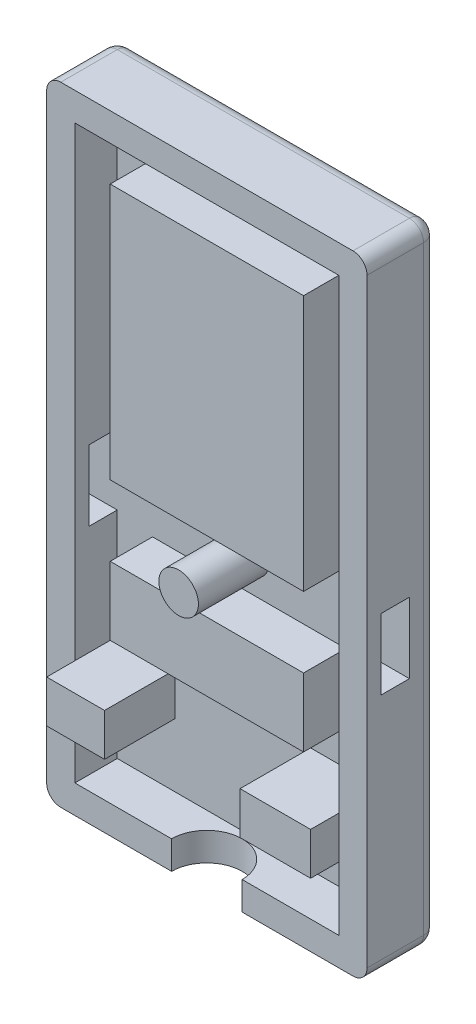
SolidWorks part; units mm, degrees
ref_plane "Front Plane" through (0, 0, 0) normal (0, 0, 1) x (1, 0, 0)
ref_plane "Top Plane" through (0, 0, 0) normal (0, 1, 0) x (1, 0, 0)
ref_plane "Right Plane" through (0, 0, 0) normal (1, 0, 0) x (0, 0, -1)
sketch "Sketch1" plane through (0, 0, 0) normal (0, 0, 1) x (1, 0, 0)
  line L1 (-11.35, 22.25) -> (11.35, 22.25)
  line L2 (-11.35, 22.25) -> (-11.35, -22.25)
  line L3 (-11.35, -22.25) -> (11.35, -22.25)
  line L4 (11.35, 22.25) -> (11.35, -22.25)
  line L5 (-11.35, 22.25) -> (11.35, -22.25) construction
  line L6 (-11.35, -22.25) -> (11.35, 22.25) construction
  point P0 (0, 0)
  dimension "D1" = 22.7
  dimension "D2" = 44.5
extrude "Boss-Extrude1" add sketch "Sketch1" along normal blind 2
sketch "Sketch2" plane through (0, 0, 2) normal (0, 0, 1) x (1, 0, 0)
  line L1 (-11.35, 22.25) -> (11.35, 22.25)
  line L2 (-11.35, 22.25) -> (-11.35, -22.25)
  line L3 (-11.35, -22.25) -> (11.35, -22.25)
  line L4 (11.35, 22.25) -> (11.35, -22.25)
  line L5 (-9.35, 20.25) -> (9.35, 20.25)
  line L6 (-9.35, 20.25) -> (-9.35, -20.25)
  line L7 (-9.35, -20.25) -> (9.35, -20.25)
  line L8 (9.35, 20.25) -> (9.35, -20.25)
  dimension "D1" = 2
  dimension "D2" = 2
  dimension "D3" = 2
  dimension "D4" = 2
extrude "Boss-Extrude2" add sketch "Sketch2" along normal blind 3
sketch "Sketch3" plane through (0, 0, 2) normal (0, 0, 1) x (1, 0, 0)
  line L0 (9.35, 20.25) -> (-9.35, 20.25) construction
  line L1 (-6.85, 19.25) -> (6.85, 19.25)
  line L2 (-6.85, 19.25) -> (-6.85, -12.75)
  line L3 (-6.85, -12.75) -> (6.85, -12.75)
  line L4 (6.85, 19.25) -> (6.85, -12.75)
  line L5 (9.35, -20.25) -> (9.35, 20.25) construction
  line L12 (-6.85, -12.75) -> (6.85, -12.75)
  line L15 (9.35, -13.15) -> (9.35, -15.75)
  line L16 (-9.35, 20.25) -> (-9.35, -20.25) construction
  line L17 (-9.35, -15.75) -> (-9.35, -13.15)
  line L19 (-6.85, -12.75) -> (-6.85, -7.5079)
  line L21 (-9.35, -12.75) -> (9.35, -12.75)
  line L22 (9.35, -12.75) -> (9.35, -13.15)
  line L23 (-9.35, -13.15) -> (-9.35, -12.75)
  line L24 (-9.35, -12.75) -> (-4.35, -12.75)
  line L25 (9.35, -15.75) -> (4.35, -15.75)
  line L26 (9.35, -12.75) -> (4.35, -12.75)
  line L27 (-4.35, -12.75) -> (-4.35, -15.75)
  line L28 (4.35, -12.75) -> (4.35, -15.75)
  line L29 (-4.35, -15.75) -> (-9.35, -15.75)
  line L31 (-6.85, -12.75) -> (-6.85, -7.15)
  line L40 (-6.85, -7.5079) -> (-3.65, -7.5079)
  line L41 (-3.65, -7.5079) -> (-3.65, -4.3079)
  line L42 (-3.65, -4.3079) -> (-6.85, -4.3079)
  line L43 (-6.85, -4.3079) -> (-6.85, -7.5079)
  line L44 (-5.25, -5.9079) -> (-9.35, -5.9079)
  line L45 (-5.25, -5.9079) -> (-5.25, -20.25)
  line L46 (-9.35, -20.25) -> (9.35, -20.25) construction
  circle A0 centre (0, -2.9) radius 1.4
  circle A1 centre (-5.25, -5.9079) radius 1.6
  line M9 (-9.35, 20.25) -> (-9.35, -20.25)
  line M11 (9.35, -20.25) -> (9.35, 20.25)
  dimension "D1" = 13.7
  dimension "D2" = 32
  dimension "D3" = 1
  dimension "D4" = 5
  dimension "D5" = 5
  dimension "D6" = 5.6
  dimension "D7" = 3.2
  dimension "D8" = 3.2
  dimension "D9" = 14.3421
  dimension "D10" = 4.1
extrude "Boss-Extrude3" add sketch "Sketch3" along normal blind 5 contours A0 | L29 L27 L3 L21 M9 | L3 L28 L25 L21 M11
sketch "Sketch4" plane through (-9.35, 0, 0) normal (1, 0, 0) x (0, 0, -1)
  line L0 (0, -22.25) -> (0, 22.25) construction
  line L8 (-4, 0) -> (-4, -2.5)
  line L10 (-2, 0) -> (-2, -2.5)
  line L11 (-4, 0) -> (-2, 0)
  line L12 (-4, 0) -> (-4, -5)
  line L13 (-4, -5) -> (-2, -5)
  line L14 (-2, 0) -> (-2, -5)
  dimension "D1" = 2
  dimension "D3" = 2.5
  dimension "D5" = 5
extrude "Cut-Extrude1" cut sketch "Sketch4" against normal through all
sketch "Sketch8" plane through (9.35, 0, 0) normal (-1, 0, 0) x (0, 0, 1)
  line L5 (2, -2.5) -> (2, 0)
  line L8 (4, -2.5) -> (4, 0)
  line L10 (4, 0) -> (4, -5) construction
  line L11 (2, 0) -> (4, 0)
  line L12 (2, 0) -> (2, -5)
  line L13 (2, -5) -> (4, -5)
  line L14 (4, 0) -> (4, -5)
  dimension "D1" = 5
  dimension "D4" = 2
extrude "Cut-Extrude2" cut sketch "Sketch8" against normal through all contours L14 L8 L11 L5 L12 L13
fillet "Fillet2" radius 1 8 edges at (0, 22.25, 0) (11.35, 22.25, 2.5) (11.35, 0, 0) (11.35, -22.25, 2.5) (0, -22.25, 0) (-11.35, -22.25, 2.5) (-11.35, 0, 0) (-11.35, 22.25, 2.5)
sketch "Sketch12" plane through (0, 0, 2) normal (0, 0, 1) x (1, 0, 0)
  line L0 (9.35, 20.25) -> (-9.35, 20.25) construction
  line L1 (-6.85, 17.75) -> (6.85, 17.75)
  line L2 (-6.85, 17.75) -> (-6.85, -0.4)
  line L3 (-6.85, -0.4) -> (6.85, -0.4)
  line L4 (6.85, 17.75) -> (6.85, -0.4)
  line L5 (-6.85, -5.4) -> (6.85, -5.4)
  line L6 (-6.85, -5.4) -> (-6.85, -10.25)
  line L7 (-6.85, -10.25) -> (6.85, -10.25)
  line L8 (6.85, -5.4) -> (6.85, -10.25)
  line L9 (4.35, -12.75) -> (9.35, -12.75) construction
  line L10 (9.35, -12.75) -> (9.35, 20.25) construction
  line L11 (-9.35, 20.25) -> (-9.35, 0) construction
  line L12 (-9.35, 20.25) -> (-9.35, -12.75) construction
  circle A0 centre (0, -2.9) radius 1.4 construction
  dimension "D1" = 2.5
  dimension "D2" = 2.5
  dimension "D3" = 2.5
  dimension "D4" = 2.5
  dimension "D5" = 2.5
  dimension "D6" = 2.5
  dimension "D7" = 2.5
  dimension "D8" = 2.5
extrude "Boss-Extrude8" add sketch "Sketch12" along normal blind 3
sketch "Sketch13" plane through (0, -20.25, 0) normal (0, 1, 0) x (1, 0, 0)
  line L0 (10.35, -5) -> (-10.35, -5) construction
  line L1 (-2.5, -5) -> (2.5, -5)
  arc A0 (2.5, -5) -> (-2.5, -5) centre (0, -5) ccw
  dimension "D1" = 5
extrude "Cut-Extrude3" cut sketch "Sketch13" against normal through all
